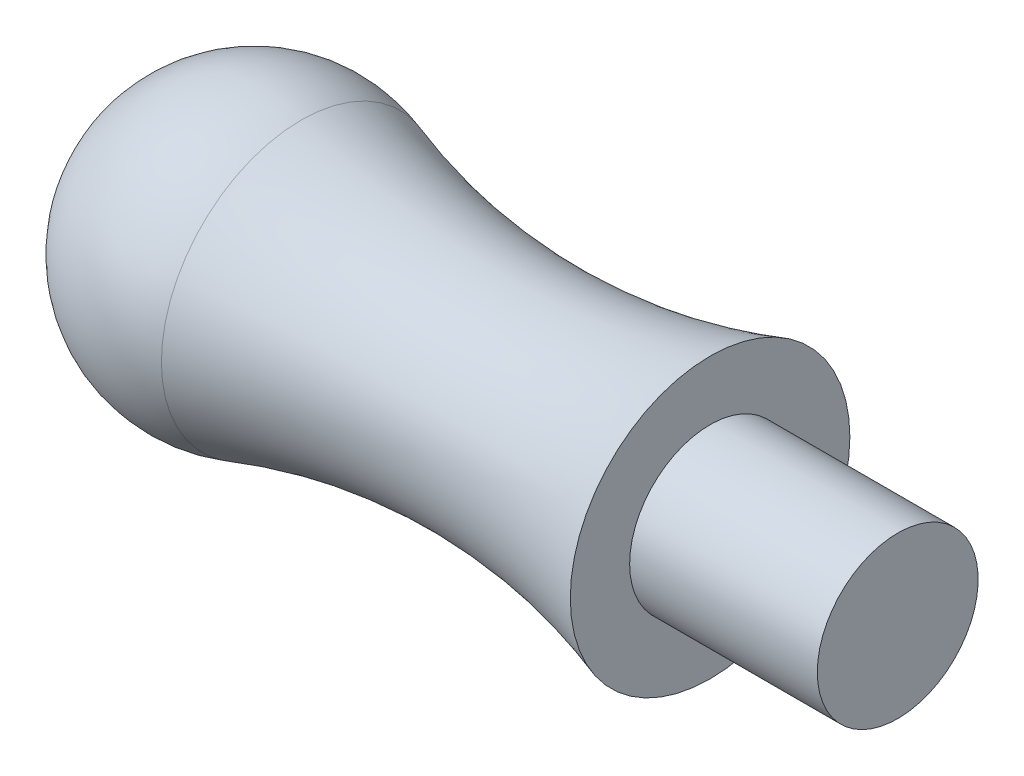
SolidWorks part; units mm, degrees
material "Plain Carbon Steel"
ref_plane "Front Plane" through (0, 0, 0) normal (0, 0, 1) x (1, 0, 0)
ref_plane "Top Plane" through (0, 0, 0) normal (0, 1, 0) x (1, 0, 0)
ref_plane "Right Plane" through (0, 0, 0) normal (1, 0, 0) x (0, 0, -1)
sketch "Sketch1" plane through (0, 0, 0) normal (0, 0, 1) x (1, 0, 0)
  line L0 (0, 0) -> (24, 0)
  line L1 (24, 0) -> (24, 3)
  line L2 (24, 3) -> (17, 3)
  line L3 (17, 3) -> (17, 5.2149)
  line L4 (0, 0) -> (-5.5, 0)
  arc A0 (17, 5.2149) -> (1.7477, 5.2149) centre (9.3738, 27.9711) cw
  arc A1 (1.7477, 5.2149) -> (-5.5, 0) centre (0, 0) ccw
  dimension "D4" = 5.5
  dimension "D5" = 24
  dimension "D1" = 24
  dimension "D2" = 3
  dimension "D3" = 7
revolve "Revolve1" add sketch "Sketch1" angle 360 about L0
cosmetic thread "Cosmetic Thread1"
